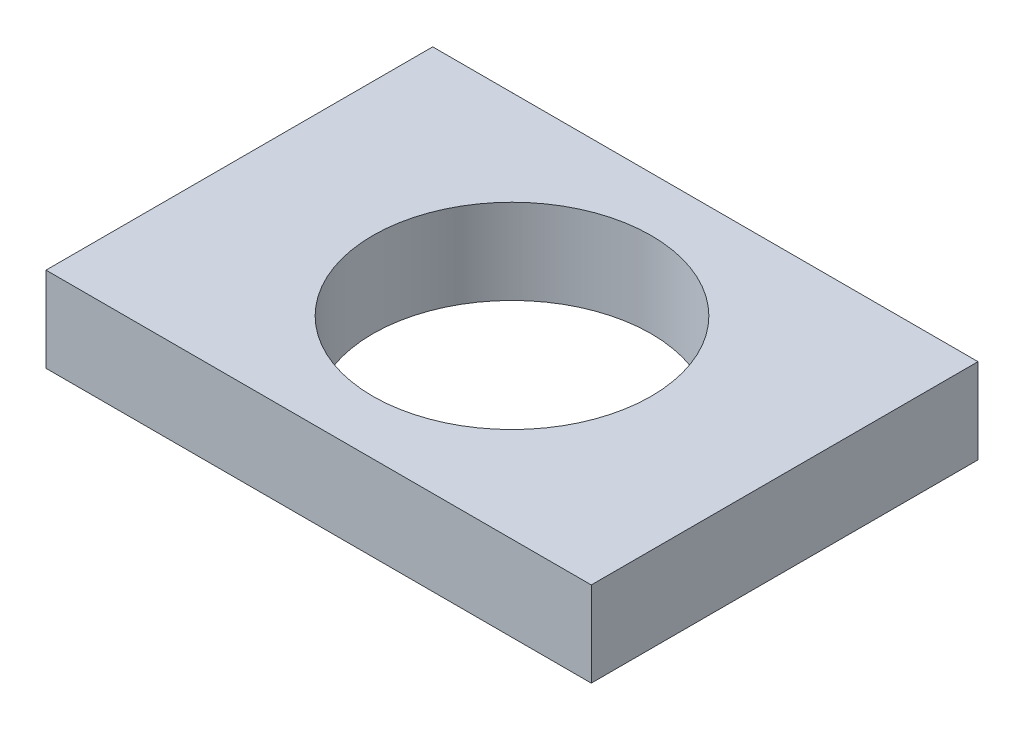
SolidWorks part; units mm, degrees
ref_plane "Front Plane" through (0, 0, 0) normal (0, 0, 1) x (1, 0, 0)
ref_plane "Top Plane" through (0, 0, 0) normal (0, 1, 0) x (1, 0, 0)
ref_plane "Right Plane" through (0, 0, 0) normal (1, 0, 0) x (0, 0, -1)
sketch "Sketch1" plane through (0, 0, 0) normal (0, 1, 0) x (1, 0, 0)
  line L1 (-10.575, 7.5) -> (10.575, 7.5)
  line L2 (-10.575, 7.5) -> (-10.575, -7.5)
  line L3 (-10.575, -7.5) -> (10.575, -7.5)
  line L4 (10.575, 7.5) -> (10.575, -7.5)
  line L5 (-10.575, 7.5) -> (10.575, -7.5) construction
  line L6 (-10.575, -7.5) -> (10.575, 7.5) construction
  point P0 (0, 0)
extrude "Boss-Extrude2" add sketch "Sketch1" along normal blind 3.3
sketch "Sketch3" plane through (0, 3.3, 0) normal (0, 1, 0) x (1, 0, 0)
  circle A0 centre (0, 0) radius 5.4
extrude "Cut-Extrude2" cut sketch "Sketch3" against normal blind 3.45
